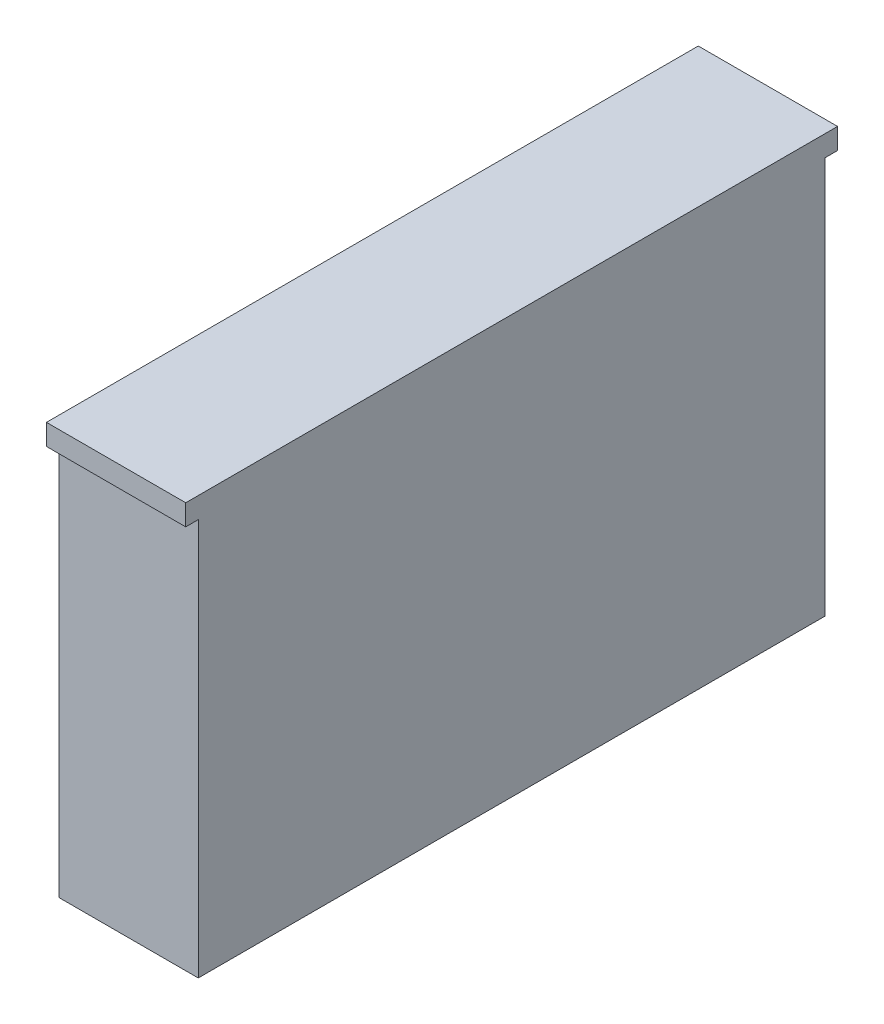
SolidWorks part; units mm, degrees
ref_plane "Alzado" through (0, 0, 0) normal (0, 0, 1) x (1, 0, 0)
ref_plane "Planta" through (0, 0, 0) normal (0, 1, 0) x (1, 0, 0)
ref_plane "Vista lateral" through (0, 0, 0) normal (1, 0, 0) x (0, 0, -1)
sketch "Croquis2" plane through (0, 0, 0) normal (1, 0, 0) x (0, 0, -1)
  line L1 (225, -150) -> (-225, -150)
  line L2 (225, -150) -> (225, 150)
  line L3 (225, 150) -> (-225, 150)
  line L4 (-225, -150) -> (-225, 150)
  line L5 (225, -150) -> (-225, 150) construction
  line L6 (225, 150) -> (-225, -150) construction
  point P0 (0, 0)
  dimension "D1" = 300
  dimension "D2" = 450
extrude "Saliente-Extruir1" add sketch "Croquis2" along normal blind 100
sketch "Croquis3" plane through (0, 0, 0) normal (-1, 0, 0) x (0, 0, 1)
  line L0 (-85.1737, 98.5116) -> (-2.5894, 8.4513) construction
  line L1 (-822.5697, 83.8671) -> (1.4303, 83.8671) construction
sketch "Croquis4" plane through (0, 0, -225) normal (0, 0, -1) x (-1, 0, 0)
  line L0 (-100, 150) -> (0, 150) construction
  line L5 (-100, 150) -> (0, 150)
  line L6 (0, 150) -> (0, 135)
  line L7 (0, -150) -> (0, 150) construction
  line L8 (0, 135) -> (-100, 135)
  line L9 (-100, -150) -> (-100, 150) construction
  line L10 (-100, 135) -> (-100, 150)
  point P0 (-79.3167, 150)
  dimension "D1" = 15
extrude "Saliente-Extruir2" add sketch "Croquis4" along normal blind 9
sketch "Croquis5" plane through (0, 0, 225) normal (0, 0, 1) x (1, 0, 0)
  line L1 (0, 150) -> (100, 150)
  line L2 (100, 150) -> (100, 135)
  line L3 (100, 135) -> (0, 135)
  line L4 (0, 135) -> (0, 150)
extrude "Saliente-Extruir3" add sketch "Croquis5" along normal blind 9
sketch "Croquis6" plane through (0, 0, -225) normal (0, 0, -1) x (-1, 0, 0)
  line L0 (-45.7416, -114.9273) -> (182.2584, -114.9273) construction
sketch "Croquis7" plane through (0, 0, -225) normal (0, 0, -1) x (-1, 0, 0)
  line L0 (-17.8265, -149.264) -> (210.1735, -149.264) construction
  line L1 (-208.937, -73.3363) -> (-75.6037, -73.3363) construction
sketch "Croquis8" plane through (0, -150, 0) normal (0, -1, 0) x (1, 0, 0)
  line L0 (-86.3236, 82.273) -> (47.0097, 82.273) construction
sketch "Croquis9" plane through (0, 0, 0) normal (-1, 0, 0) x (0, 0, 1)
  line L0 (-125.693, -85.6081) -> (-32.3597, -85.6081) construction
  line L1 (-6.4935, -67.8695) -> (70.1732, -67.8695) construction
  line L2 (152.8037, -355.4711) -> (413.4704, -355.4711) construction
  line L3 (-130.5297, -82.3842) -> (-101.1964, -82.3842) construction
  line L4 (-8.9602, -85.357) -> (21.0398, -85.357) construction
  line L5 (114.5501, -73.4511) -> (143.2168, -73.4511) construction
  line L6 (110.0139, 77.8263) -> (139.3472, 77.8263) construction
